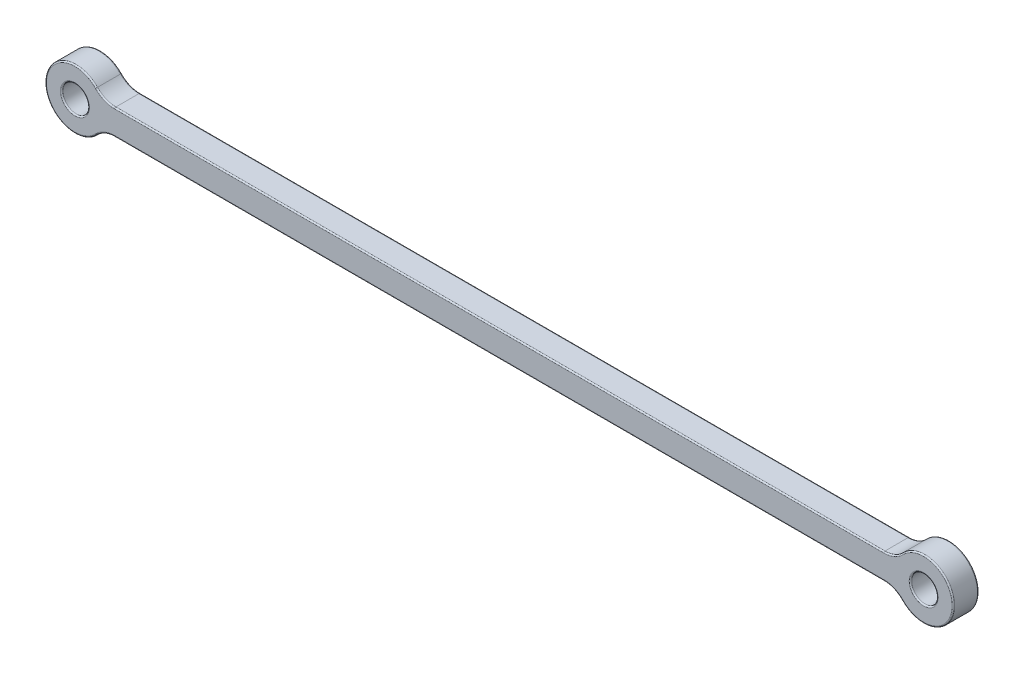
SolidWorks part; units mm, degrees
ref_plane "Front Plane" through (0, 0, 0) normal (0, 0, 1) x (1, 0, 0)
ref_plane "Top Plane" through (0, 0, 0) normal (0, 1, 0) x (1, 0, 0)
ref_plane "Right Plane" through (0, 0, 0) normal (1, 0, 0) x (0, 0, -1)
sketch "Sketch1" plane through (0, 0, 0) normal (0, 0, 1) x (1, 0, 0)
  line L0 (0, 0) -> (100, 0) construction
  line L1 (0, 3.5) -> (100, 3.5) construction
  line L2 (0, -3.5) -> (100, -3.5) construction
  line L3 (50, 0) -> (50, -3.5) construction
  line L5 (96.8377, -1.5) -> (3.1623, -1.5)
  line L6 (96.8377, -1.5) -> (96.8377, 1.5) construction
  line L7 (96.8377, 1.5) -> (3.1623, 1.5)
  line L8 (3.1623, -1.5) -> (3.1623, 1.5) construction
  line L9 (96.8377, -1.5) -> (3.1623, 1.5) construction
  line L10 (96.8377, 1.5) -> (3.1623, -1.5) construction
  arc A0 (0, 3.5) -> (0, -3.5) centre (0, 0) ccw construction
  arc A1 (100, -3.5) -> (100, 3.5) centre (100, 0) ccw construction
  circle A2 centre (0, 0) radius 3.5
  circle A3 centre (0, 0) radius 1.55
  circle A4 centre (100, 0) radius 1.55
  circle A5 centre (100, 0) radius 3.5
  point P3 (50, 0)
  dimension "D3" = 3.1
  dimension "D1" = 100
  dimension "D2" = 7
  dimension "D4" = 3
extrude "Boss-Extrude1" add sketch "Sketch1" along normal mid plane 3 contours A2 A3 | L5 A5 L7 A2 | A5 A4
fillet "Fillet1" radius 3 4 edges at (96.8377, -1.5, 0) (3.1623, -1.5, 0) (96.8377, 1.5, 0) (3.1623, 1.5, 0)
fillet "Fillet3" radius 0.15 20 edges at (101.55, 0, 1.5) (101.55, 0, -1.5) (1.55, 0, 1.5) (1.55, 0, -1.5) (3.5137, 1.7404, 1.5) (3.5137, 1.7404, -1.5) (-3.5, 0, -1.5) (-3.5, 0, 1.5) (3.5137, -1.7404, 1.5) (3.5137, -1.7404, -1.5) (50, -1.5, -1.5) (50, -1.5, 1.5) (96.4863, -1.7404, 1.5) (96.4863, -1.7404, -1.5) (103.5, 0, 1.5) (103.5, 0, -1.5) (96.4863, 1.7404, 1.5) (96.4863, 1.7404, -1.5) (50, 1.5, 1.5) (50, 1.5, -1.5)
